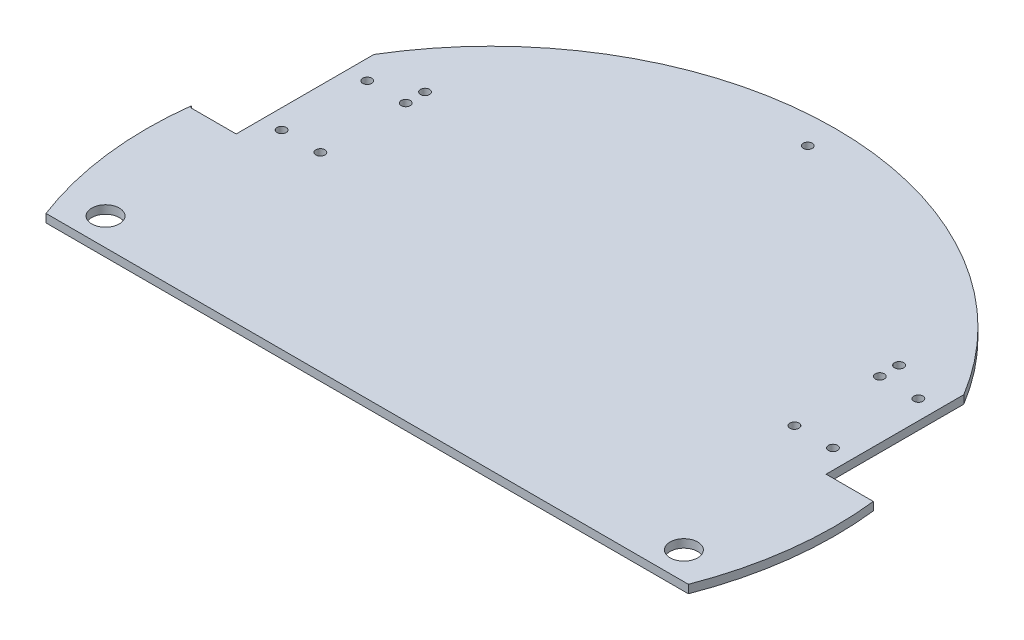
SolidWorks part; units mm, degrees
ref_plane "Front Plane" through (0, 0, 0) normal (0, 0, 1) x (1, 0, 0)
ref_plane "Top Plane" through (0, 0, 0) normal (0, 1, 0) x (1, 0, 0)
ref_plane "Right Plane" through (0, 0, 0) normal (1, 0, 0) x (0, 0, -1)
sketch "Sketch2" plane through (0, 0, 0) normal (0, 1, 0) x (1, 0, 0)
  circle A0 centre (-17.8077, -0.8549) radius 125
  dimension "D1" = 250
extrude "Boss-Extrude1" add sketch "Sketch2" along normal blind 3
sketch "Sketch3" plane through (0, 0, 0) normal (0, -1, 0) x (1, 0, 0)
  line L0 (-134.4267, 45.8549) -> (98.8114, 45.8549)
  circle A0 centre (-17.8077, 0.8549) radius 125 construction
  circle A1 centre (-17.8077, 0.8549) radius 125
  circle M2 centre (-17.8077, 0.8549) radius 125
  dimension "D1" = 45
extrude "Cut-Extrude1" cut sketch "Sketch3" against normal blind 3 contours L0 M2
sketch "Sketch4" plane through (0, 0, 0) normal (0, -1, 0) x (-1, 0, 0)
  line L0 (134.4267, -45.8549) -> (-98.8114, -45.8549) construction
  line L1 (124.8812, 63.6451) -> (124.8812, 13.6451)
  line L2 (124.8812, 13.6451) -> (141.3575, 13.6451)
  line L3 (141.3575, 13.6451) -> (159.3776, 40.4813)
  line L4 (159.3776, 40.4813) -> (124.8812, 63.6451)
  line L5 (-89.1923, 63.7671) -> (-89.1923, 13.7671)
  line L6 (-89.1923, 13.7671) -> (-106.3342, 13.7671)
  line L7 (-106.3342, 13.7671) -> (-114.0798, 54.5963)
  line L8 (-114.0798, 54.5963) -> (-89.1923, 63.7671)
  circle A0 centre (117.8077, 54.1451) radius 1.65
  circle A1 centre (117.8812, 23.1452) radius 1.65
  circle A2 centre (103.8077, 54.1451) radius 1.65
  circle A3 centre (103.8077, 23.1451) radius 1.65
  arc A4 (134.4267, -45.8549) -> (-98.8114, -45.8549) centre (17.8077, -0.8549) ccw construction
  circle A5 centre (-68.1923, 54.2671) radius 1.65
  circle A6 centre (-82.1923, 54.2671) radius 1.65
  circle A7 centre (-82.1923, 23.2671) radius 1.65
  circle A8 centre (-68.1923, 23.2671) radius 1.65
  circle A9 centre (122.8077, -35.8549) radius 5
  circle A10 centre (-87.1923, -35.8549) radius 5
  dimension "D1" = 3.3
  dimension "D3" = 31
  dimension "D8" = 14
  dimension "D10" = 105
  dimension "D11" = 105
  dimension "D2" = 100
  dimension "D4" = 31
  dimension "D5" = 0
  dimension "D6" = 14
  dimension "D7" = 100
  dimension "D9" = 100
  dimension "D12" = 10
  dimension "D13" = 10
  dimension "D14" = 50
  dimension "D15" = 7
  dimension "D16" = 7
  dimension "D17" = 14
  dimension "D18" = 31
  dimension "D19" = 0
  dimension "D20" = 50
  dimension "D21" = 9.5001
  dimension "D22" = 9.5
extrude "Cut-Extrude2" cut sketch "Sketch4" against normal blind 10
sketch "Sketch6" plane through (0, 0, 0) normal (0, -1, 0) x (-1, 0, 0)
  line L0 (124.8812, 13.6451) -> (-89.1923, 13.7671)
  circle A0 centre (103.8077, 61.1451) radius 1.65
  circle A1 centre (-68.1923, 61.2671) radius 1.65
  circle A2 centre (103.8077, 54.1451) radius 1.65 construction
  circle A3 centre (103.8077, 54.1451) radius 1.65 construction
  circle A4 centre (-68.1923, 54.2671) radius 1.65 construction
  circle A5 centre (17.3812, 113.7064) radius 1.65
  point P6 (0, 0)
  dimension "D1" = 3.3
  dimension "D2" = 3.3
  dimension "D5" = 7
  dimension "D6" = 0
  dimension "D8" = 107.5
  dimension "D9" = 100
  dimension "D3" = 0
  dimension "D4" = 7
  dimension "D7" = 214.0736
extrude "Cut-Extrude3" cut sketch "Sketch6" against normal blind 100 contours A0 | A5 | A1
